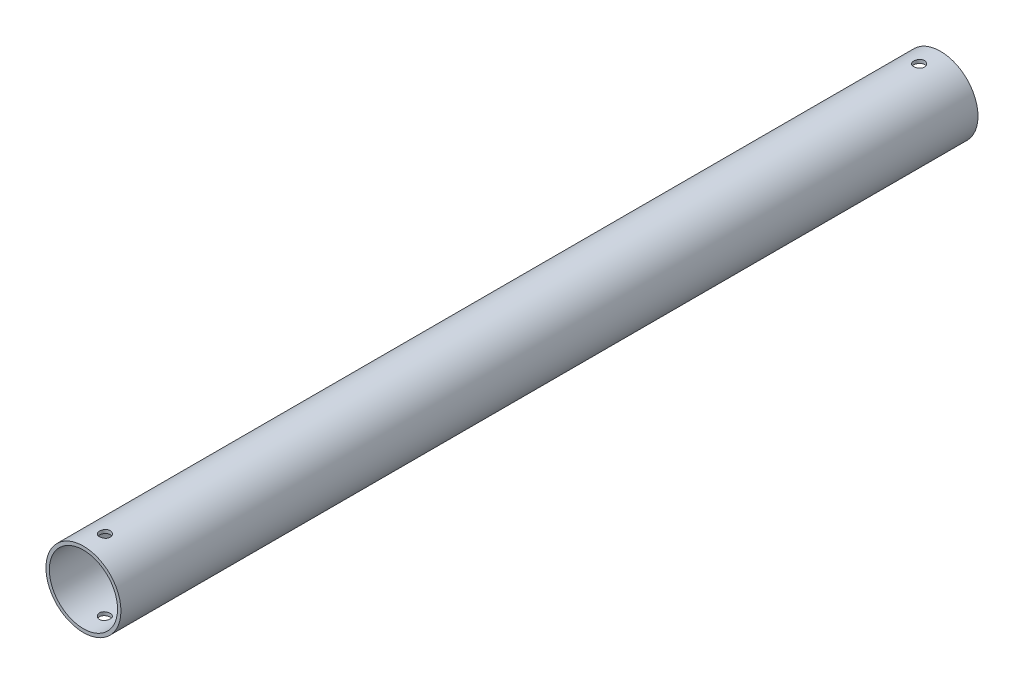
SolidWorks part; units mm, degrees
material "1060 Alloy"
ref_plane "Front Plane" through (0, 0, 0) normal (0, 0, 1) x (1, 0, 0)
ref_plane "Top Plane" through (0, 0, 0) normal (0, 1, 0) x (1, 0, 0)
ref_plane "Right Plane" through (0, 0, 0) normal (1, 0, 0) x (0, 0, -1)
sketch "Sketch1" plane through (0, 0, 0) normal (0, 0, 1) x (1, 0, 0)
  circle A0 centre (0, 0) radius 15.9125
  circle A1 centre (0, 0) radius 17.5
  dimension "D1" = 35
  dimension "D2" = 31.825
extrude "Boss-Extrude1" add sketch "Sketch1" along normal mid plane 400
sketch "Sketch3" plane through (0, 0, 0) normal (0, 1, 0) x (1, 0, 0)
  line L0 (0, 200) -> (0, 180) construction
  line L1 (17.5, 200) -> (-17.5, 200) construction
  dimension "D1" = 20
sketch "Esquisse1" plane through (0, 0, 0) normal (0, 1, 0) x (1, 0, 0)
  line L0 (15.9125, 200) -> (-15.9125, 200) construction
  line L1 (-19.25, 0) -> (19.25, 0) construction
  circle A0 centre (0, 190) radius 2.5
  circle A1 centre (0, -190) radius 2.5
  dimension "D2" = 5
  dimension "D1" = 10
extrude "Enlèv. mat.-Extru.1" cut sketch "Esquisse1" against normal through all both and the other way through all
equation "\"tubeOutDiameter\" = 35mm"
equation "\"wheelShaftDiameter\"= 12mm"
equation "\"wheelThickness\"= 135mm"
equation "\"BearingDiameter\"= 20mm"
equation "\"BearingThickness\"= 10mm"
equation "\"D2@Sketch1\"=\"tubeOutDiameter\"-0.125in"
equation "\"D1@Sketch1\"=\"tubeOutDiameter\""
